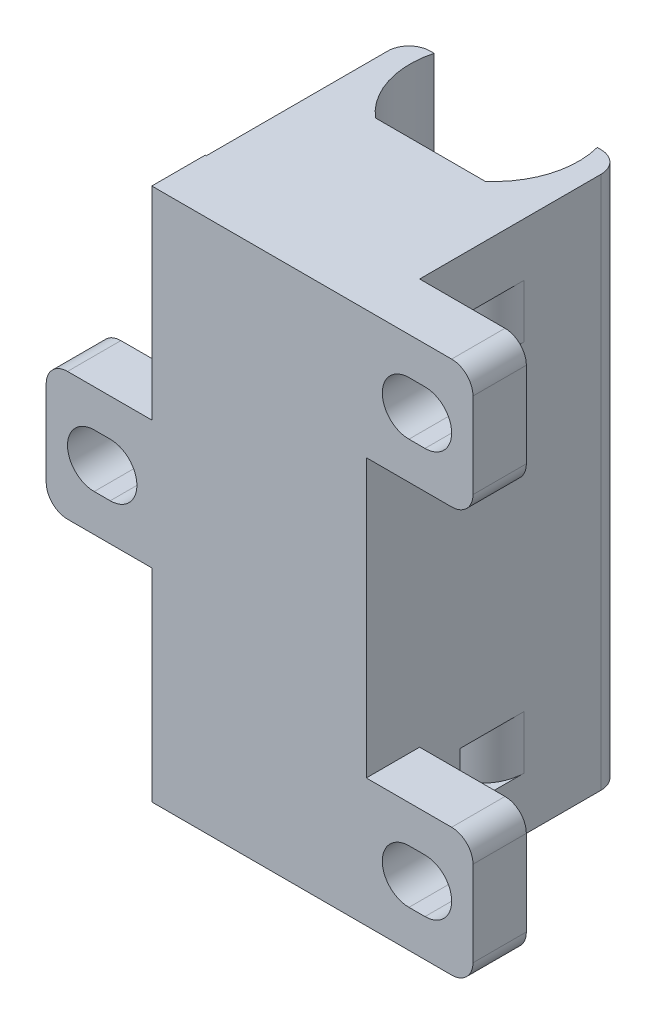
SolidWorks part; units mm, degrees
ref_plane "Front Plane" through (0, 0, 0) normal (0, 0, 1) x (1, 0, 0)
ref_plane "Top Plane" through (0, 0, 0) normal (0, 1, 0) x (1, 0, 0)
ref_plane "Right Plane" through (0, 0, 0) normal (1, 0, 0) x (0, 0, -1)
sketch "Sketch1" plane through (0, 0, 0) normal (0, 1, 0) x (1, 0, 0)
  line L0 (-5.277, 0) -> (34.723, 0)
  line L1 (-5.277, 0) -> (-5.277, 5)
  line L2 (14.723, 0) -> (14.723, 27.5) construction
  line L3 (7.0804, 24) -> (4.723, 24)
  line L4 (4.723, 24) -> (4.723, 5)
  line L5 (4.723, 5) -> (-5.277, 5)
  line L6 (24.723, 5) -> (34.723, 5)
  line L7 (24.723, 24) -> (24.723, 5)
  line L8 (22.3657, 24) -> (24.723, 24)
  line L9 (34.723, 0) -> (34.723, 5)
  arc A0 (22.3657, 24) -> (7.0804, 24) centre (14.723, 22) cw
  point P3 (14.723, 22)
  dimension "D1" = 22
  dimension "D2" = 10
  dimension "D6" = 7.9
  dimension "D3" = 2
  dimension "D4" = 5
  dimension "D5" = 20
extrude "Boss-Extrude1" add sketch "Sketch1" along normal blind 50
ref_plane "Plane1" through (0, 0, -16) normal (0, 0, -1) x (-1, 0, 0)
sketch "Sketch2" plane through (0, 0, -16) normal (0, 0, -1) x (-1, 0, 0)
  line L0 (-7.0804, 50) -> (-7.0804, 0) construction
  line L1 (-22.3657, 50) -> (-7.0804, 50)
  line L2 (-22.3657, 50) -> (-22.3657, 48)
  line L3 (-22.3657, 48) -> (-7.0804, 48)
  line L4 (-7.0804, 50) -> (-7.0804, 48)
  line L6 (-22.3657, 0) -> (-7.0804, 0)
  line L7 (-22.3657, 0) -> (-22.3657, 2)
  line L8 (-22.3657, 2) -> (-7.0804, 2)
  line L9 (-7.0804, 0) -> (-7.0804, 2)
  dimension "D1" = 2
  dimension "D2" = 2
extrude "Boss-Extrude2" add sketch "Sketch2" against normal blind 10
fillet "Fillet1" radius 2 6 edges at (-5.277, 50, -2.5) (-5.277, 0, -2.5) (34.723, 50, -2.5) (34.723, 0, -2.5) (4.723, 25, -24) (24.723, 25, -24)
sketch "Sketch3" plane through (0, 0, -5) normal (0, 0, -1) x (-1, 0, 0)
  line L0 (-0.723, 25) -> (0.777, 25) construction
  line L1 (-0.723, 27.5) -> (0.777, 27.5)
  line L2 (-30.223, 44) -> (-28.723, 44) construction
  line L3 (-32.723, 50) -> (-24.723, 50) construction
  line L4 (-30.223, 46.5) -> (-28.723, 46.5)
  line L5 (-30.223, 41.5) -> (-28.723, 41.5)
  line L6 (-34.723, 48) -> (-34.723, 2) construction
  line L7 (-24.723, 50) -> (-24.723, 0) construction
  line L8 (-34.723, 38) -> (-24.723, 38)
  line L9 (-34.723, 38) -> (-34.723, 12)
  line L10 (-34.723, 12) -> (-24.723, 12)
  line L11 (-24.723, 38) -> (-24.723, 12)
  line L12 (-30.223, 6) -> (-28.723, 6) construction
  line L13 (-30.223, 8.5) -> (-28.723, 8.5)
  line L14 (-30.223, 3.5) -> (-28.723, 3.5)
  line L15 (-24.723, 0) -> (-34.723, 0) construction
  line L16 (-0.723, 22.5) -> (0.777, 22.5)
  line L17 (-4.723, 50) -> (3.277, 50) construction
  line L18 (5.277, 48) -> (5.277, 2) construction
  line L19 (-4.723, 0) -> (5.277, 0) construction
  line L20 (5.277, 31) -> (-4.6206, 31)
  line L21 (5.277, 31) -> (5.277, 50)
  line L22 (5.277, 50) -> (-4.6206, 50)
  line L23 (-4.6206, 31) -> (-4.6206, 50)
  line L24 (-4.6206, 19) -> (5.277, 19)
  line L25 (-4.6206, 19) -> (-4.6206, 0)
  line L26 (-4.6206, 0) -> (5.277, 0)
  line L27 (5.277, 19) -> (5.277, 0)
  arc A0 (-30.223, 46.5) -> (-30.223, 41.5) centre (-30.223, 44) ccw
  arc A1 (-30.223, 8.5) -> (-30.223, 3.5) centre (-30.223, 6) ccw
  arc A2 (-28.723, 3.5) -> (-28.723, 8.5) centre (-28.723, 6) ccw
  arc A3 (-0.723, 27.5) -> (-0.723, 22.5) centre (-0.723, 25) ccw
  arc A4 (-28.723, 41.5) -> (-28.723, 46.5) centre (-28.723, 44) ccw
  arc A5 (0.777, 22.5) -> (0.777, 27.5) centre (0.777, 25) ccw
  point P4 (-29.473, 44)
  point P19 (-29.473, 6)
  point P28 (0.027, 25)
  dimension "D1" = 6
  dimension "D5" = 6
  dimension "D2" = 4.5
  dimension "D3" = 6
  dimension "D4" = 6
  dimension "D6" = 4.5
  dimension "D7" = 25
  dimension "D8" = 4.5
  dimension "D9" = 6
  dimension "D10" = 6
extrude "Cut-Extrude1" cut sketch "Sketch3" against normal through all
sketch "Sketch4" plane through (4.723, 0, 0) normal (-1, 0, 0) x (0, 0, 1)
  line L0 (-22, 50) -> (-5, 50) construction
  line L1 (-10.8027, 45) -> (-8.8027, 45)
  line L2 (-10.8027, 45) -> (-10.8027, 40)
  line L3 (-10.8027, 40) -> (-8.8027, 40)
  line L4 (-8.8027, 45) -> (-8.8027, 40)
  line L5 (-10.8027, 10) -> (-8.8027, 10)
  line L6 (-10.8027, 10) -> (-10.8027, 5)
  line L7 (-10.8027, 5) -> (-8.8027, 5)
  line L8 (-8.8027, 10) -> (-8.8027, 5)
  dimension "D1" = 5
  dimension "D2" = 2
extrude "Cut-Extrude2" cut sketch "Sketch4" against normal through all
fillet "Fillet2" radius 4 4 edges at (4.723, 42.5, -10.8027) (4.723, 7.5, -10.8027) (24.723, 7.5, -10.8027) (24.723, 42.5, -10.8027)
fillet "Fillet3" radius 2 4 edges at (-5.277, 31, -2.5) (-5.277, 19, -2.5) (34.723, 12, -2.5) (34.723, 38, -2.5)
